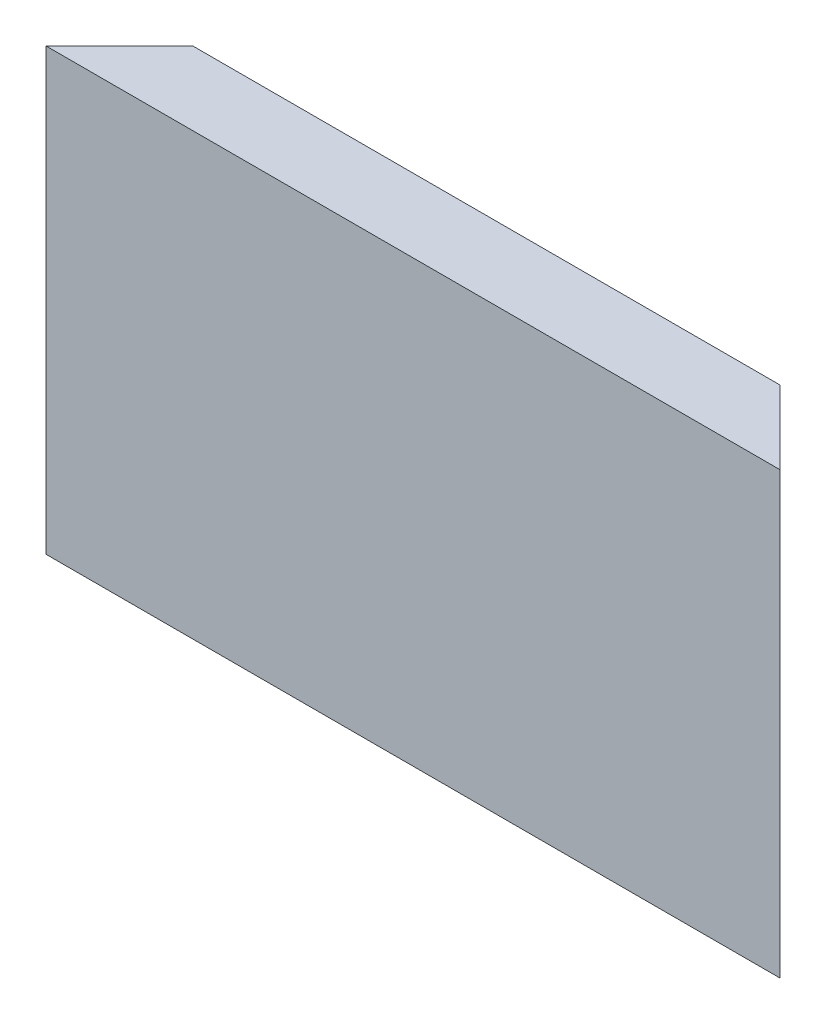
SolidWorks part; units mm, degrees
ref_plane "Front Plane" through (0, 0, 0) normal (0, 0, 1) x (1, 0, 0)
ref_plane "Top Plane" through (0, 0, 0) normal (0, 1, 0) x (1, 0, 0)
ref_plane "Right Plane" through (0, 0, 0) normal (1, 0, 0) x (0, 0, -1)
sketch "Sketch1" plane through (0, 0, 0) normal (0, 0, 1) x (1, 0, 0)
  line L1 (-25, 15) -> (25, 15)
  line L2 (-25, 15) -> (-25, -15)
  line L3 (-25, -15) -> (25, -15)
  line L4 (25, 15) -> (25, -15)
  line L5 (-25, 15) -> (25, -15) construction
  line L6 (-25, -15) -> (25, 15) construction
  point P0 (0, 0)
  dimension "D1" = 30
  dimension "D2" = 50
extrude "Boss-Extrude1" add sketch "Sketch1" along normal blind 5
sketch "Sketch4" plane through (0, 15, 0) normal (0, 1, 0) x (1, 0, 0)
  line L0 (-25, -5) -> (-20, 0)
  line L1 (25, -5) -> (20, 0)
  line L2 (25, -5) -> (-25, -5) construction
  line L3 (25, -5) -> (25, 0) construction
  line L4 (25, 0) -> (-25, 0) construction
  line L5 (-25, -5) -> (-25, 0) construction
  line L6 (25, -5) -> (25, 0)
  line L7 (25, 0) -> (20, 0)
  line L8 (-25, -5) -> (-25, 0)
  line L9 (-20, 0) -> (-25, 0)
  dimension "D1" = 45
  dimension "D2" = 45
extrude "Cut-Extrude3" cut sketch "Sketch4" against normal through all both
sketch "Sketch5" plane through (0, 0, 0) normal (1, 0, 0) x (0, 0, -1)
  line L0 (-5, -15) -> (0, -10)
  line L1 (-5, -15) -> (-5, 15) construction
  line L2 (0, -15) -> (0, 15) construction
  line L3 (0, -15) -> (0, -10)
  line L4 (0, -15) -> (-5, -15) construction
  line L5 (0, -15) -> (-5, -15)
  dimension "D1" = 45
extrude "Cut-Extrude4" cut sketch "Sketch5" against normal through all both and the other way through all
